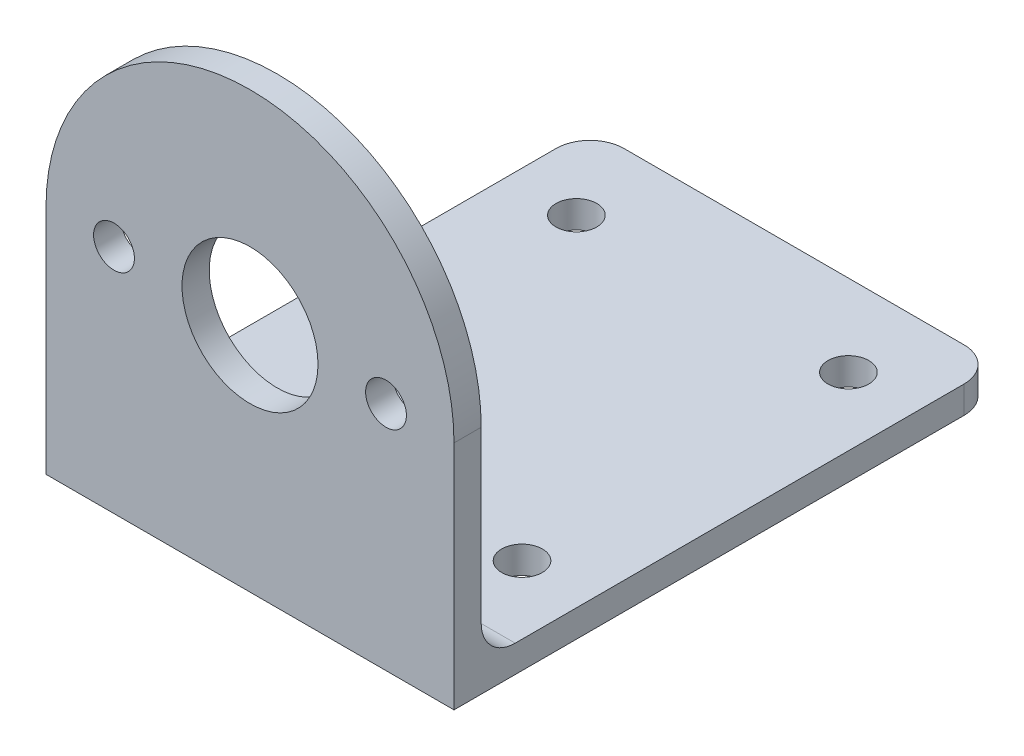
SolidWorks part; units mm, degrees
ref_plane "前视基准面" through (0, 0, 0) normal (0, 0, 1) x (1, 0, 0)
ref_plane "上视基准面" through (0, 0, 0) normal (0, 1, 0) x (1, 0, 0)
ref_plane "右视基准面" through (0, 0, 0) normal (1, 0, 0) x (0, 0, -1)
sketch "草图1" plane through (0, 0, 0) normal (0, 1, 0) x (1, 0, 0)
  line L0 (0, 5.3981) -> (0, -6.5093) construction
  line L1 (-6.5556, 0) -> (6.1296, 0) construction
  line L3 (-12.5, 40) -> (12.5, 40)
  line L4 (-15, 37.5) -> (-15, 0)
  line L5 (-15, 0) -> (15, 0)
  line L6 (15, 37.5) -> (15, 0)
  arc A0 (15, 37.5) -> (12.5, 40) centre (12.5, 37.5) ccw
  arc A1 (-15, 37.5) -> (-12.5, 40) centre (-12.5, 37.5) cw
  point P13 (-15, 40)
  dimension "D4" = 2.5
  dimension "D1" = 15
  dimension "D2" = 15
  dimension "D3" = 40
extrude "凸台-拉伸1" add sketch "草图1" along normal blind 2
sketch "草图2" plane through (0, 0, 0) normal (0, 0, 1) x (1, 0, 0)
  line L0 (-15, 1) -> (-15, 17)
  line L1 (-15, 2) -> (-15, 0) construction
  line L2 (15, 0) -> (15, 17)
  line L3 (-15, 2) -> (15, 2) construction
  arc A0 (15, 17) -> (-15, 17) centre (0, 17) ccw
  circle A1 centre (0, 17) radius 5
  line M6 (15, 2) -> (-15, 2)
  dimension "D2" = 10
  dimension "D1" = 15
extrude "凸台-拉伸2" add sketch "草图2" against normal blind 2 contours L2 A0 L0 A1 M6
fillet "圆角1" radius 2.5 1 edges at (0, 2, -2)
sketch "草图3" plane through (0, 0, 0) normal (0, -1, 0) x (1, 0, 0)
  line L7 (16.5, 0) -> (-16.5, 0) construction
  circle A0 centre (10, -10) radius 1.5
  circle A1 centre (-10, -10) radius 1.5
  circle A2 centre (-10, -34) radius 1.5
  circle A3 centre (10, -34) radius 1.5
  dimension "D5" = 3
  dimension "D6" = 3
  dimension "D7" = 3
  dimension "D8" = 3
  dimension "D1" = 10
  dimension "D2" = 10
extrude "切除-拉伸1" cut sketch "草图3" against normal blind 12
sketch "草图4" plane through (0, 0, 0) normal (0, 0, 1) x (1, 0, 0)
  line L0 (0, -17.6) -> (0, 17.6) construction
  circle A0 centre (10, 17) radius 1.5
  circle A1 centre (-10, 17) radius 1.5
  dimension "D1" = 3
  dimension "D2" = 10
extrude "切除-拉伸2" cut sketch "草图4" against normal blind 10
